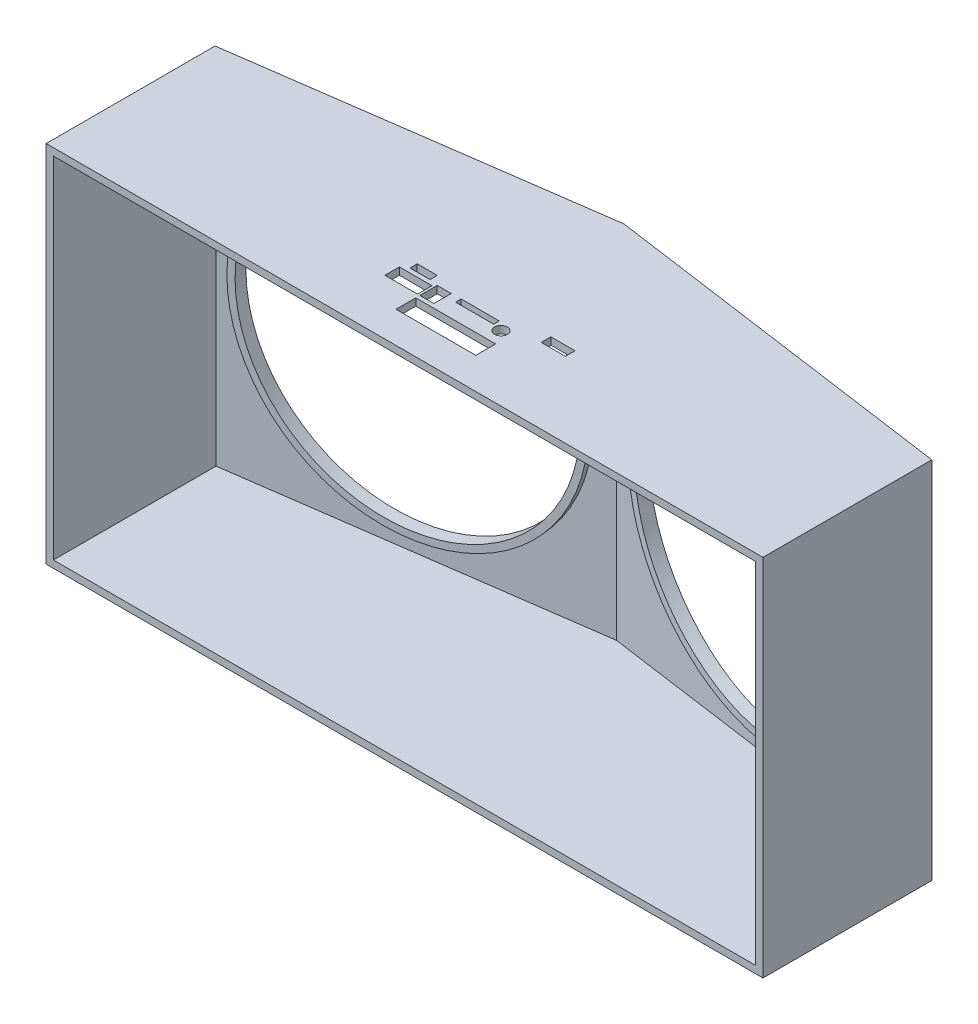
SolidWorks part; units mm, degrees
ref_plane "Alzado" through (0, 0, 0) normal (0, 0, 1) x (1, 0, 0)
ref_plane "Planta" through (0, 0, 0) normal (0, 1, 0) x (1, 0, 0)
ref_plane "Vista lateral" through (0, 0, 0) normal (1, 0, 0) x (0, 0, -1)
sketch "Croquis2" plane through (0, 0, 0) normal (0, 1, 0) x (1, 0, 0)
  line L0 (0, 0) -> (0, 90.3029) construction
  line L1 (0, 90.3029) -> (148.5402, 69.4269)
  line L2 (0, 90.3029) -> (-148.5402, 69.4269)
  line L4 (-148.5402, 72.4564) -> (-0.4175, 93.2737)
  line L7 (148.5402, 72.4564) -> (0.4175, 93.2737)
  line L11 (-148.5402, 69.4269) -> (-148.5402, 72.4564)
  line L12 (148.5402, 69.4269) -> (148.5402, 72.4564)
  line L14 (-0.4175, 93.2737) -> (0.4175, 93.2737)
  point P8 (-148.5402, 69.4269)
  point P11 (148.5402, 69.4269)
  point P15 (0, 93.2737)
  dimension "D1" = 150
  dimension "D2" = 150
  dimension "D3" = 82
  dimension "D4" = 82
  dimension "D5" = 3
  dimension "D6" = 3
extrude "Saliente-Extruir1" add sketch "Croquis2" along normal blind 145
sketch "Croquis3" plane through (12.4454, 0, -88.5538) normal (-0.1392, 0, 0.9903) x (0.9903, 0, 0.1392)
  line L0 (-12.5677, 145) -> (137.4323, 0) construction
  line L1 (-12.5677, 0) -> (137.4323, 145) construction
  circle A0 centre (62.4323, 72.5) radius 66.25
  circle A1 centre (62.4323, 72.5) radius 63.25
  dimension "D1" = 132.5
  dimension "D2" = 126.5
extrude "Saliente-Extruir2" add sketch "Croquis3" along normal blind 2.3
sketch "Croquis5" plane through (-12.4454, 0, -88.5538) normal (0.1392, 0, 0.9903) x (0.9903, 0, -0.1392)
  line L0 (-137.4323, 145) -> (12.5677, 0) construction
  line L1 (-137.4323, 0) -> (12.5677, 145) construction
  circle A0 centre (-62.4323, 72.5) radius 66.25
  circle A1 centre (-62.4323, 72.5) radius 63.25
  dimension "D1" = 126.5
  dimension "D2" = 132.5
extrude "Saliente-Extruir3" add sketch "Croquis5" along normal blind 2.3
sketch "Croquis6" plane through (-12.4454, 0, -88.5538) normal (0.1392, 0, 0.9903) x (0.9903, 0, -0.1392)
  circle A0 centre (-62.4323, 72.5) radius 63.25
extrude "Cortar-Extruir3" cut sketch "Croquis6" against normal through all
sketch "Croquis7" plane through (12.4454, 0, -88.5538) normal (-0.1392, 0, 0.9903) x (0.9903, 0, 0.1392)
  circle A0 centre (62.4323, 72.5) radius 63.25
extrude "Cortar-Extruir4" cut sketch "Croquis7" against normal through all
sketch "Croquis9" plane through (0, 0, 0) normal (0, -1, 0) x (1, 0, 0)
  line L0 (-148.5402, -72.4564) -> (-0.4175, -93.2737)
  line L2 (-148.5402, -72.4564) -> (-148.5402, -2.4564)
  line L3 (-148.5402, -2.4564) -> (148.5402, -2.4564)
  line L4 (148.5402, -72.4564) -> (148.5402, -2.4564)
  line L5 (-0.4175, -93.2737) -> (0.4175, -93.2737)
  line L6 (0.4175, -93.2737) -> (148.5402, -72.4564)
  point P0 (-148.5402, -72.4564)
  point P1 (148.5402, -72.4564)
  dimension "D1" = 70
extrude "Saliente-Extruir4" add sketch "Croquis9" along normal blind 3
sketch "Croquis10" plane through (0, -3, 0) normal (0, -1, 0) x (1, 0, 0)
  line L0 (148.5402, -2.4564) -> (-148.5402, -2.4564) construction
  line L1 (-148.5402, -72.4564) -> (-145.5402, -72.4564)
  line L2 (-148.5402, -72.4564) -> (-148.5402, -2.4564)
  line L3 (-148.5402, -2.4564) -> (-145.5402, -2.4564)
  line L4 (-145.5402, -72.4564) -> (-145.5402, -2.4564)
  line L6 (148.5402, -2.4564) -> (145.5402, -2.4564)
  line L7 (148.5402, -2.4564) -> (148.5402, -72.4564)
  line L8 (148.5402, -72.4564) -> (145.5402, -72.4564)
  line L9 (145.5402, -2.4564) -> (145.5402, -72.4564)
  dimension "D1" = 3
  dimension "D2" = 3
extrude "Saliente-Extruir5" add sketch "Croquis10" against normal up to surface (148 mm away) up to face at (0, 145, -80.0881)
sketch "Croquis11" plane through (0, 145, 0) normal (0, 1, 0) x (1, 0, 0)
  line L0 (148.5402, 72.4564) -> (0.4175, 93.2737)
  line L1 (148.5402, 2.4564) -> (-148.5402, 2.4564)
  line L2 (148.5402, 2.4564) -> (148.5402, 72.4564)
  line L4 (-148.5402, 2.4564) -> (-148.5402, 72.4564)
  line L5 (0.4175, 93.2737) -> (-0.4175, 93.2737)
  line L6 (-0.4175, 93.2737) -> (-148.5402, 72.4564)
extrude "Saliente-Extruir6" add sketch "Croquis11" along normal blind 3
sketch "Croquis12" plane through (0, 145, 0) normal (0, -1, 0) x (1, 0, 0)
  line L0 (0, -2.4564) -> (0, -15.4564) construction
  line L2 (-145.5402, -2.4564) -> (145.5402, -2.4564) construction
  line L3 (-16.55, -15.4564) -> (16.55, -15.4564)
  line L4 (0, -33.6564) -> (0, -23.6564) construction
  line L5 (-37.4, -33.6564) -> (37.4, -33.6564) construction
  line L6 (-16.55, -15.4564) -> (-16.55, -23.6564)
  line L7 (-16.55, -23.6564) -> (16.55, -23.6564)
  line L8 (16.55, -23.6564) -> (16.55, -15.4564)
  line L9 (-10.75, -25.3564) -> (-16.55, -25.3564)
  line L14 (-10.75, -25.3564) -> (-10.75, -32.5564)
  line L15 (-10.75, -32.5564) -> (-16.55, -32.5564)
  line L16 (-16.55, -25.3564) -> (-16.55, -32.5564)
  line L17 (-6.75, -30.3564) -> (9.05, -30.3564)
  line L18 (-6.75, -30.3564) -> (-6.75, -32.6564)
  line L19 (-6.75, -32.6564) -> (9.05, -32.6564)
  line L20 (9.05, -30.3564) -> (9.05, -32.6564)
  line L21 (-17.55, -25.3564) -> (-31.05, -25.3564)
  line L22 (-17.55, -25.3564) -> (-17.55, -31.3564)
  line L23 (-17.55, -31.3564) -> (-31.05, -31.3564)
  line L24 (-31.05, -25.3564) -> (-31.05, -31.3564)
  line L25 (-28.45, -33.1564) -> (-20.15, -33.1564)
  line L26 (-28.45, -33.1564) -> (-28.45, -36.1564)
  line L27 (-28.45, -36.1564) -> (-20.15, -36.1564)
  line L28 (-20.15, -33.1564) -> (-20.15, -36.1564)
  line L29 (25.45, -33.6564) -> (35.45, -33.6564)
  line L30 (25.45, -33.6564) -> (25.45, -37.6564)
  line L31 (25.45, -37.6564) -> (35.45, -37.6564)
  line L32 (35.45, -33.6564) -> (35.45, -37.6564)
  circle A0 centre (12.9, -29.5176) radius 2.65
  point P9 (0, -15.4564)
  point P13 (0, -33.6564)
  point P31 (-24.3, -31.3564)
  point P32 (-24.3, -33.1564)
  dimension "D19" = 5.3
  dimension "D1" = 33.1
  dimension "D2" = 13
  dimension "D3" = 8.2
  dimension "D4" = 10
  dimension "D5" = 5.8
  dimension "D6" = 1.1
  dimension "D7" = 7.2
  dimension "D8" = 0
  dimension "D9" = 1
  dimension "D10" = 4
  dimension "D11" = 15.8
  dimension "D12" = 2.3
  dimension "D13" = 1
  dimension "D14" = 13.5
  dimension "D15" = 6
  dimension "D16" = 1.8
  dimension "D17" = 3
  dimension "D18" = 8.3
  dimension "D20" = 3.65
  dimension "D21" = 16.4
  dimension "D22" = 10
  dimension "D23" = 4
extrude "Cortar-Extruir5" cut sketch "Croquis12" against normal blind 10
